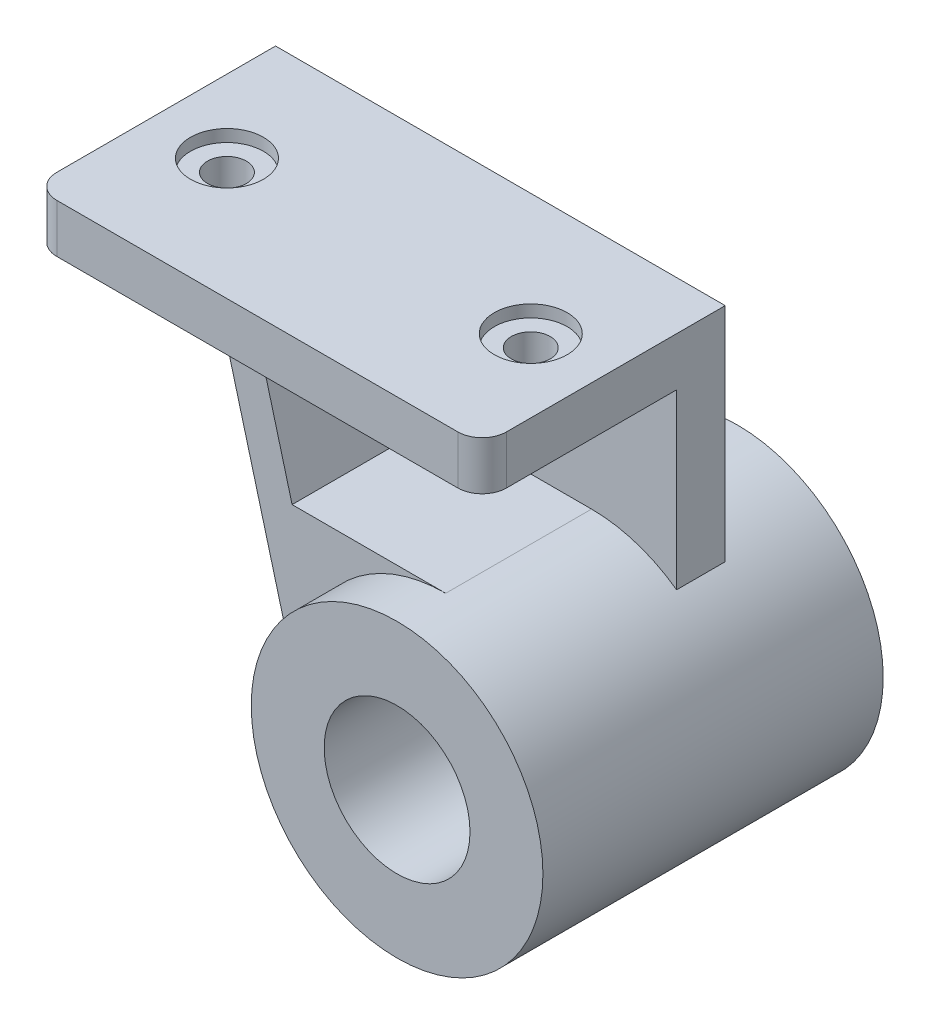
SolidWorks part; units mm, degrees
material "AISI 1020"
ref_plane "Front Plane" through (0, 0, 0) normal (0, 0, 1) x (1, 0, 0)
ref_plane "Top Plane" through (0, 0, 0) normal (0, 1, 0) x (1, 0, 0)
ref_plane "Right Plane" through (0, 0, 0) normal (1, 0, 0) x (0, 0, -1)
sketch "Sketch1" plane through (0, 0, 0) normal (0, 0, 1) x (1, 0, 0)
  circle A0 centre (0, 0) radius 30
  circle A1 centre (0, 0) radius 60
  dimension "D1" = 60
  dimension "D2" = 120
extrude "Boss-Extrude1" add sketch "Sketch1" along normal mid plane 140
ref_plane "Plane1" through (0, 0, 50) normal (0, 0, 1) x (1, 0, 0)
sketch "Sketch4" plane through (0, 0, 50) normal (0, 0, 1) x (1, 0, 0)
  line L0 (-94.2705, 120) -> (-79.2705, 120)
  line L1 (0, 60) -> (-63.1935, 60)
  line L2 (-63.1935, 60) -> (-79.2705, 120)
  line L3 (-94.2705, 120) -> (-57.9555, -15.5291)
  arc A0 (0, 60) -> (-57.9555, -15.5291) centre (0, 0) ccw
  circle A1 centre (0, 0) radius 60 construction
  dimension "D1" = 120
  dimension "D2" = 105
  dimension "D3" = 15
extrude "Boss-Extrude4" add sketch "Sketch4" against normal blind 60
sketch "Sketch7" plane through (0, 0, -10) normal (0, 0, -1) x (-1, 0, 0)
  line L0 (150, 120) -> (-35, 120)
  line L1 (150, 120) -> (50.2406, -32.8007)
  line L2 (-35, 120) -> (-35, 48.734)
  line L3 (79.2705, 120) -> (94.2705, 120) construction
  arc A0 (50.2406, -32.8007) -> (-35, 48.734) centre (0, 0) ccw
  arc A1 (57.9555, -15.5291) -> (0, 60) centre (0, 0) ccw construction
  dimension "D1" = 185
  dimension "D2" = 35
extrude "Boss-Extrude5" add sketch "Sketch7" along normal blind 20
sketch "Sketch8" plane through (0, 120, 0) normal (0, 1, 0) x (1, 0, 0)
  line L0 (-150, 30) -> (-150, -60)
  line L2 (-140, -70) -> (25, -70)
  line L3 (35, -60) -> (35, 30)
  line L4 (-150, 30) -> (35, 30) construction
  line L5 (35, 30) -> (-150, 30)
  line L6 (35, 30) -> (35, 10) construction
  line L7 (-150, 30) -> (-150, 10) construction
  line L8 (-60, -70) -> (60, -70) construction
  arc A0 (25, -70) -> (35, -60) centre (25, -60) ccw
  arc A1 (-150, -60) -> (-140, -70) centre (-140, -60) ccw
  dimension "D1" = 10
extrude "Boss-Extrude6" add sketch "Sketch8" along normal blind 20
hole_wizard "CBORE for M12 Hex Head Screw1" positions "Sketch10" profile "Sketch11" counterbore size "M12" standard "ISO"
sketch "Sketch10" plane through (0, 140, 0) normal (0, 1, 0) x (1, 0, 0)
  line L0 (-150, 30) -> (-150, -60) construction
  line L2 (35, 30) -> (-150, 30) construction
  line L3 (35, -60) -> (35, 30) construction
  point P0 (-120, -20)
  point P2 (5, -20)
  dimension "D1" = 30
  dimension "D2" = 50
  dimension "D3" = 30
  dimension "D4" = 50
sketch "Sketch11" plane through (-120, 140, 20) normal (1, 0, 0) x (0, 0, 1)
  line L0 (0, 0) -> (0, 24.8069)
  line L1 (0, 24.8069) -> (8, 20)
  line L2 (8, 20) -> (8, 5)
  line L3 (8, 5) -> (15, 5)
  line L4 (15, 5) -> (15, 0)
  line L5 (15, 0) -> (0, 0)
  line L10 (0, 24.8069) -> (-8, 20) construction
  line L11 (0, -6.35) -> (0, 107.95) construction
  dimension "Hole Dia." = 16
  dimension "Hole Depth" = 20
  dimension "C'Bore Dia." = 30
  dimension "C'Bore Depth" = 5
  dimension "Drill Angle" = 118
